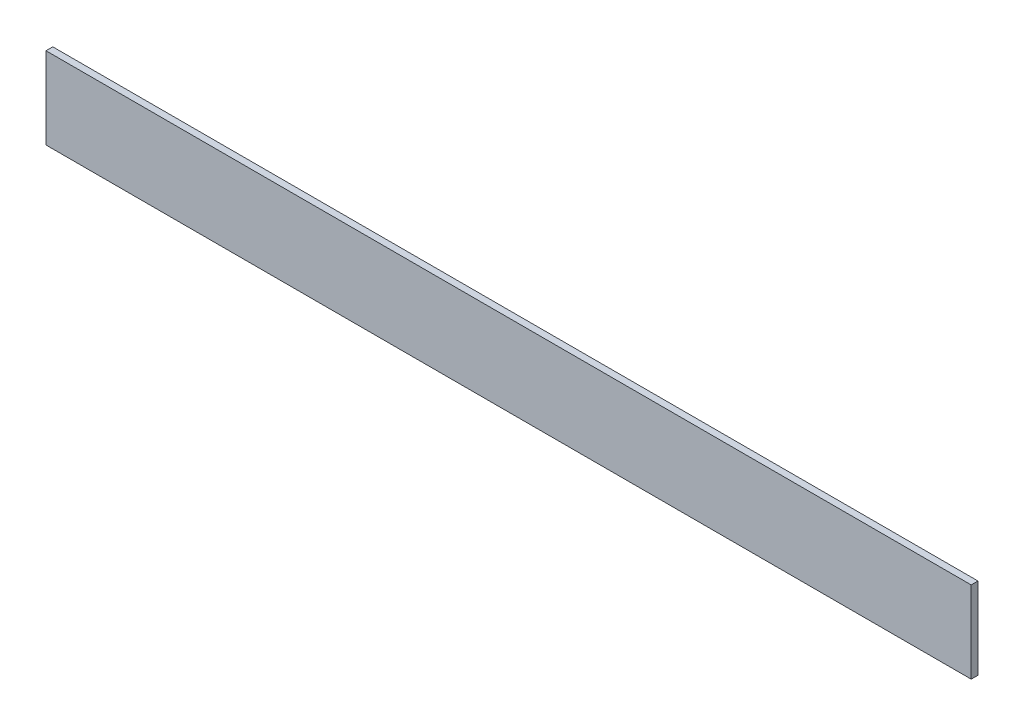
SolidWorks part; units mm, degrees
material "PVC 0.007 Plasticized"
ref_plane "Front Plane" through (0, 0, 0) normal (0, 0, 1) x (1, 0, 0)
ref_plane "Top Plane" through (0, 0, 0) normal (0, 1, 0) x (1, 0, 0)
ref_plane "Right Plane" through (0, 0, 0) normal (1, 0, 0) x (0, 0, -1)
sketch "Sketch1" plane through (0, 0, 0) normal (1, 0, 0) x (0, 0, -1)
  line L1 (-3.175, -38.1) -> (3.175, -38.1)
  line L2 (-3.175, -38.1) -> (-3.175, 38.1)
  line L3 (-3.175, 38.1) -> (3.175, 38.1)
  line L4 (3.175, -38.1) -> (3.175, 38.1)
  line L5 (-3.175, -38.1) -> (3.175, 38.1) construction
  line L6 (-3.175, 38.1) -> (3.175, -38.1) construction
  point P0 (0, 0)
  dimension "D1" = 76.2
  dimension "D2" = 6.35
extrude "Boss-Extrude1" add sketch "Sketch1" along normal blind 863.6
equation "\"D2@Sketch1\"=1in/4"
